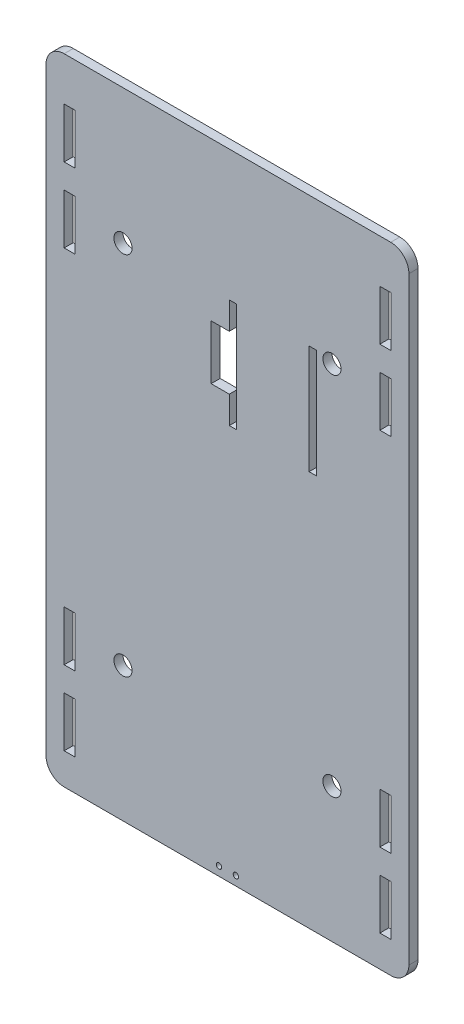
SolidWorks part; units mm, degrees
material "Pine"
ref_plane "Front Plane" through (0, 0, 0) normal (0, 0, 1) x (1, 0, 0)
ref_plane "Top Plane" through (0, 0, 0) normal (0, 1, 0) x (1, 0, 0)
ref_plane "Right Plane" through (0, 0, 0) normal (1, 0, 0) x (0, 0, -1)
sketch "Sketch1" plane through (0, 0, 0) normal (0, 0, 1) x (1, 0, 0)
  line L1 (100, 190) -> (-100, 190)
  line L3 (100, -160) -> (-100, -160)
  line L5 (-100, 190) -> (100, -160) construction
  line L6 (100, 190) -> (-100, -160) construction
  line L8 (-100, 190) -> (-100, -90)
  line L9 (100, 190) -> (100, -90)
  line L10 (-100, -90) -> (-100, -160)
  line L12 (100, -90) -> (100, -160)
  circle A0 centre (-57.5876, 115.7782) radius 5
  circle A1 centre (57.5876, 115.7782) radius 5
  circle A2 centre (57.5876, -85.7782) radius 5
  circle A3 centre (-57.5876, -85.7782) radius 5
  point P0 (0, 0)
  point P5 (0, -160)
  point P23 (0, 15)
  dimension "D8" = 10
  dimension "D1" = 160
  dimension "D2" = 350
  dimension "D9" = 100
extrude "Boss-Extrude1" add sketch "Sketch1" along normal blind 5
sketch "Sketch4" plane through (0, 0, 5) normal (0, 0, 1) x (1, 0, 0)
  line L0 (1, 73) -> (1, 58)
  line L1 (49, 118) -> (45, 118)
  line L2 (49, 118) -> (49, 58)
  line L3 (49, 58) -> (45, 58)
  line L4 (45, 118) -> (45, 58)
  line L5 (49, 118) -> (45, 58) construction
  line L6 (49, 58) -> (45, 118) construction
  line L9 (5, 118) -> (1, 118)
  line L10 (5, 118) -> (5, 58)
  line L11 (5, 58) -> (1, 58)
  line L12 (1, 118) -> (1, 103)
  line L13 (5, 118) -> (1, 58) construction
  line L14 (5, 58) -> (1, 118) construction
  line L15 (100, 190) -> (-100, 190) construction
  line L16 (100, -160) -> (100, 190) construction
  line L18 (1, 103) -> (-9, 103)
  line L20 (1, 73) -> (-9, 73)
  line L21 (-9, 103) -> (-9, 73)
  line L22 (1, 103) -> (-9, 73) construction
  line L23 (1, 73) -> (-9, 103) construction
  point P0 (47, 88)
  point P5 (3, 88)
  point P14 (-4, 88)
  dimension "D1" = 4
  dimension "D2" = 60
  dimension "D3" = 40
  dimension "D4" = 102
  dimension "D5" = 97
  dimension "D6" = 30
  dimension "D7" = 10
  dimension "D8" = 60
extrude "Cut-Extrude1" cut sketch "Sketch4" against normal blind 10
sketch "Sketch5" plane through (0, 0, 5) normal (0, 0, 1) x (1, 0, 0)
  line L0 (-100, 190) -> (-100, -160) construction
  line L1 (-90, 166) -> (-84, 166)
  line L2 (-90, 166) -> (-90, 138.35)
  line L3 (-90, 138.35) -> (-84, 138.35)
  line L4 (-84, 166) -> (-84, 138.35)
  line L5 (-90, 124.94) -> (-84, 124.94)
  line L6 (-90, 124.94) -> (-90, 97.29)
  line L7 (-90, 97.29) -> (-84, 97.29)
  line L8 (-84, 124.94) -> (-84, 97.29)
  line L9 (-90, -74.02) -> (-84, -74.02)
  line L10 (-90, -74.02) -> (-90, -101.67)
  line L11 (-90, -101.67) -> (-84, -101.67)
  line L12 (-84, -74.02) -> (-84, -101.67)
  line L13 (-90, -115.08) -> (-84, -115.08)
  line L14 (-90, -115.08) -> (-90, -142.73)
  line L15 (-90, -142.73) -> (-84, -142.73)
  line L16 (-84, -115.08) -> (-84, -142.73)
  line L17 (84, -74.02) -> (90, -74.02)
  line L18 (84, -74.02) -> (84, -101.67)
  line L19 (84, -101.67) -> (90, -101.67)
  line L20 (90, -74.02) -> (90, -101.67)
  line L21 (84, -115.08) -> (90, -115.08)
  line L22 (84, -115.08) -> (84, -142.73)
  line L23 (84, -142.73) -> (90, -142.73)
  line L24 (90, -115.08) -> (90, -142.73)
  line L25 (84, 166) -> (90, 166)
  line L26 (84, 166) -> (84, 138.35)
  line L27 (84, 138.35) -> (90, 138.35)
  line L28 (90, 166) -> (90, 138.35)
  line L29 (84, 124.94) -> (90, 124.94)
  line L30 (84, 124.94) -> (84, 97.29)
  line L31 (84, 97.29) -> (90, 97.29)
  line L32 (90, 124.94) -> (90, 97.29)
  line L33 (100, 190) -> (-100, 190) construction
  line L34 (100, -160) -> (100, 190) construction
  line L35 (100, 190) -> (-100, 190) construction
  line L36 (-100, 190) -> (-100, -160) construction
  line L37 (100, -160) -> (100, 190) construction
  line L38 (-100, -160) -> (100, -160) construction
  circle A0 centre (4.67, -155) radius 1.5
  circle A1 centre (-4.67, -155) radius 1.5
  dimension "D19" = 5
  dimension "D22" = 3
  dimension "D1" = 27.65
  dimension "D2" = 6
  dimension "D3" = 13.41
  dimension "D4" = 10
  dimension "D5" = 24
  dimension "D6" = 10
  dimension "D7" = 10
  dimension "D8" = 10
  dimension "D9" = 24
  dimension "D10" = 13.41
  dimension "D11" = 10
  dimension "D12" = 10
  dimension "D13" = 10
  dimension "D14" = 10
  dimension "D15" = 13.41
  dimension "D16" = 13.41
  dimension "D17" = 17.27
  dimension "D18" = 17.27
extrude "Cut-Extrude2" cut sketch "Sketch5" against normal through all
fillet "Fillet1" radius 10 4 edges at (100, 190, 2.5) (-100, 190, 2.5) (-100, -160, 2.5) (100, -160, 2.5)
